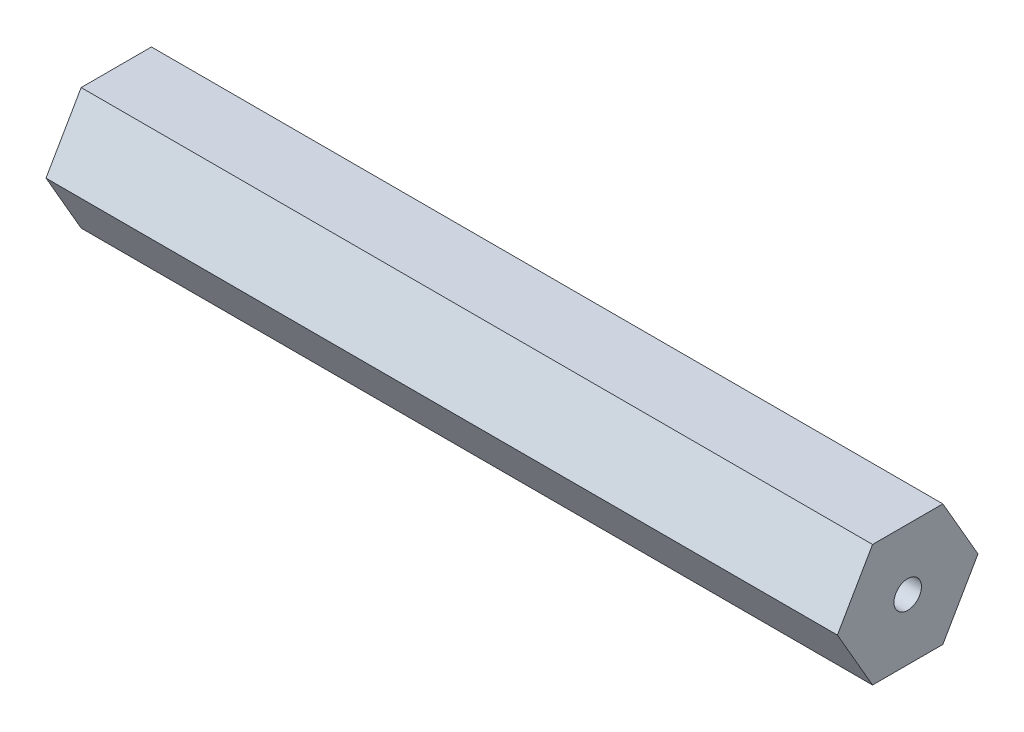
SolidWorks part; units mm, degrees
ref_plane "Front Plane" through (0, 0, 0) normal (0, 0, 1) x (1, 0, 0)
ref_plane "Top Plane" through (0, 0, 0) normal (0, 1, 0) x (1, 0, 0)
ref_plane "Right Plane" through (0, 0, 0) normal (1, 0, 0) x (0, 0, -1)
sketch "Sketch1" plane through (0, 0, 0) normal (1, 0, 0) x (0, 0, -1)
  line L0 (0, 55) -> (0, -55) construction
  line L1 (3.6662, -6.35) -> (7.3323, 0)
  line L2 (7.3323, 0) -> (3.6662, 6.35)
  line L3 (3.6662, 6.35) -> (-3.6662, 6.35)
  line L4 (-3.6662, 6.35) -> (-7.3323, 0)
  line L5 (-7.3323, 0) -> (-3.6662, -6.35)
  line L6 (-3.6662, -6.35) -> (3.6662, -6.35)
  circle A0 centre (0, 0) radius 6.35 construction
  circle A1 centre (0, 0) radius 1.4317
  dimension "D1" = 12.7
extrude "Boss-Extrude1" add sketch "Sketch1" along normal blind 82.55
